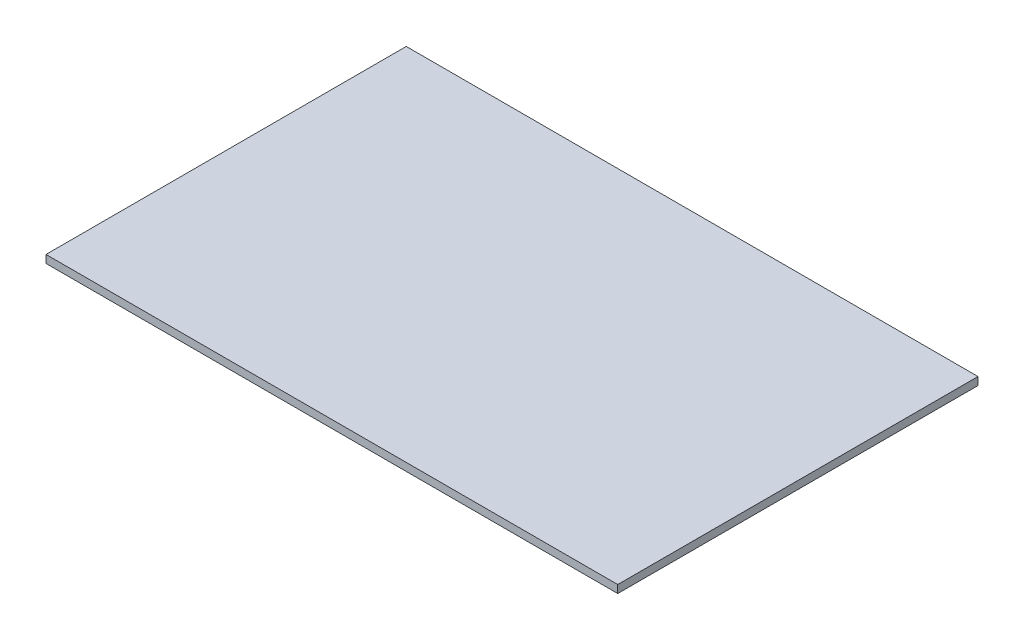
SolidWorks part; units mm, degrees
ref_plane "Alzado" through (0, 0, 0) normal (0, 0, 1) x (1, 0, 0)
ref_plane "Planta" through (0, 0, 0) normal (0, 1, 0) x (1, 0, 0)
ref_plane "Vista lateral" through (0, 0, 0) normal (1, 0, 0) x (0, 0, -1)
sketch "Croquis1" plane through (0, 0, 0) normal (0, 1, 0) x (1, 0, 0)
  line L1 (-36.5, 23) -> (36.5, 23)
  line L2 (-36.5, 23) -> (-36.5, -23)
  line L3 (-36.5, -23) -> (36.5, -23)
  line L4 (36.5, 23) -> (36.5, -23)
  line L5 (-36.5, 23) -> (36.5, -23) construction
  line L6 (-36.5, -23) -> (36.5, 23) construction
  point P0 (0, 0)
  dimension "D1" = 73
  dimension "D2" = 46
extrude "Saliente-Extruir1" add sketch "Croquis1" along normal blind 1
